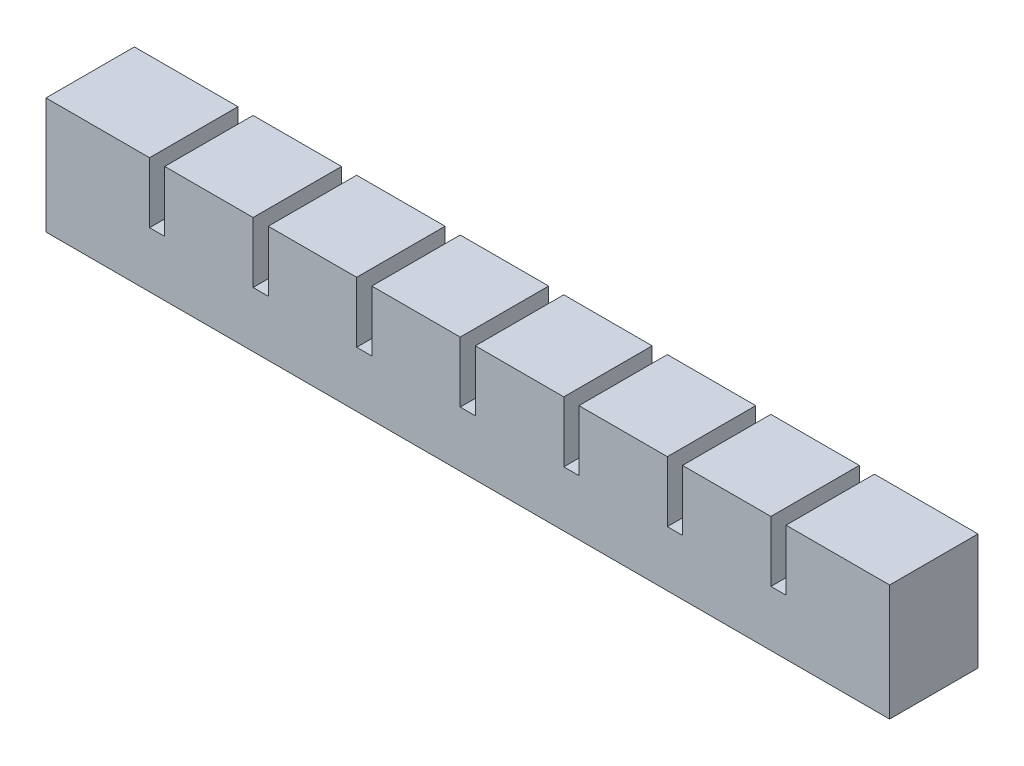
SolidWorks part; units mm, degrees
ref_plane "Front Plane" through (0, 0, 0) normal (0, 0, 1) x (1, 0, 0)
ref_plane "Top Plane" through (0, 0, 0) normal (0, 1, 0) x (1, 0, 0)
ref_plane "Right Plane" through (0, 0, 0) normal (1, 0, 0) x (0, 0, -1)
sketch "Sketch1" plane through (0, 0, 0) normal (0, 0, 1) x (1, 0, 0)
  line L1 (0, 0) -> (17.5, 0)
  line L2 (0, 0) -> (0, 17.5)
  line L3 (0, 17.5) -> (17.5, 17.5)
  line L4 (17.5, 0) -> (17.5, 17.5)
  dimension "D1" = 17.5
  dimension "D2" = 17.5
extrude "Boss-Extrude1" add sketch "Sketch1" along normal blind 17.5
sketch "Sketch2" plane through (0, 0, 0) normal (0, -1, 0) x (1, 0, 0)
  line L0 (0, 17.5) -> (0, 0) construction
  line L1 (5.5, 12) -> (12, 12)
  line L2 (5.5, 12) -> (5.5, 5.5)
  line L3 (5.5, 5.5) -> (12, 5.5)
  line L4 (12, 12) -> (12, 5.5)
  line L5 (17.5, 17.5) -> (17.5, 0) construction
  line L6 (0, 17.5) -> (17.5, 17.5) construction
  line L7 (0, 0) -> (17.5, 0) construction
  dimension "D1" = 5.5
  dimension "D2" = 5.5
  dimension "D3" = 5.5
  dimension "D4" = 5.5
extrude "Cut-Extrude1" cut sketch "Sketch2" against normal blind 12
sketch "Sketch3" plane through (17.5, 0, 0) normal (1, 0, 0) x (0, 0, -1)
  line L0 (0, 0) -> (0, 17.5) construction
  line L1 (-17.5, 0) -> (0, 0)
  line L2 (-17.5, 0) -> (-17.5, 5.5)
  line L3 (-17.5, 5.5) -> (0, 5.5)
  line L4 (0, 0) -> (0, 5.5)
  dimension "D1" = 5.5
extrude "Boss-Extrude2" add sketch "Sketch3" along normal blind 3
pattern_linear "LPattern1" count 8 spacing 20.5 along (1, 0, 0) of bodies 103
combine bodies "Combine1" operation type add bodies to combine 104 105 106 107 108 103 109 110
sketch "Sketch4" plane through (161, 0, 0) normal (1, 0, 0) x (0, 0, -1)
  line L1 (-17.5, 17.5) -> (0, 17.5)
  line L2 (-17.5, 17.5) -> (-17.5, 5.5)
  line L3 (-17.5, 5.5) -> (0, 5.5)
  line L4 (0, 17.5) -> (0, 5.5)
extrude "Boss-Extrude3" add sketch "Sketch4" along normal up to surface (3 mm away) up to face at (164, 2.75, 8.75)
sketch "Sketch5" plane through (0, 0, 0) normal (-1, 0, 0) x (0, 0, 1)
  line L1 (0, 17.5) -> (17.5, 17.5)
  line L2 (0, 17.5) -> (0, 0)
  line L3 (0, 0) -> (17.5, 0)
  line L4 (17.5, 17.5) -> (17.5, 0)
extrude "Boss-Extrude4" add sketch "Sketch5" along normal blind 3
ref_point "Point1"
sketch "Sketch6" plane through (0, 0, 0) normal (0, -1, 0) x (1, 0, 0)
  line L0 (149, 12) -> (149, 5.5) construction
  line L1 (12, 9.75) -> (149, 9.75)
  line L2 (12, 9.75) -> (12, 7.75)
  line L3 (12, 7.75) -> (149, 7.75)
  line L4 (149, 9.75) -> (149, 7.75)
  line L5 (12, 9.75) -> (149, 7.75) construction
  line L6 (12, 7.75) -> (149, 9.75) construction
  point P0 (80.5, 8.75)
  dimension "D1" = 2
extrude "Cut-Extrude2" cut sketch "Sketch6" against normal blind 2
sketch "Sketch7" plane through (0, 0, 0) normal (0, -1, 0) x (1, 0, 0)
  line L1 (-3, 17.5) -> (164, 17.5)
  line L2 (-3, 17.5) -> (-3, 0)
  line L3 (-3, 0) -> (164, 0)
  line L4 (164, 17.5) -> (164, 0)
extrude "Boss-Extrude5" add sketch "Sketch7" along normal blind 5.5
